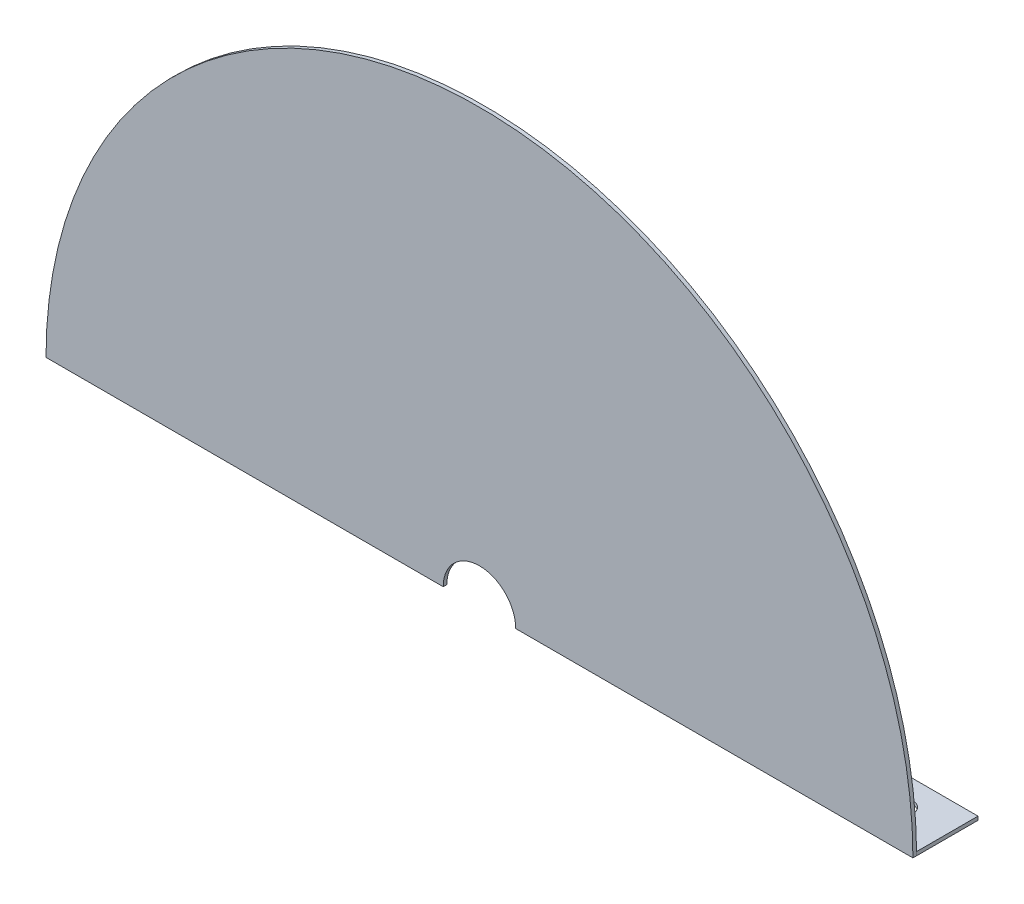
SolidWorks part; units mm, degrees
material "Plain Carbon Steel"
ref_plane "Front Plane" through (0, 0, 0) normal (0, 0, 1) x (1, 0, 0)
ref_plane "Top Plane" through (0, 0, 0) normal (0, 1, 0) x (1, 0, 0)
ref_plane "Right Plane" through (0, 0, 0) normal (1, 0, 0) x (0, 0, -1)
sketch "Plate shape" plane through (0, 0, 0) normal (0, 0, 1) x (1, 0, 0)
  line L3 (-154.3999, 0) -> (210.7061, 0) construction
  line L4 (0, 179.3189) -> (-179.3189, 179.3189)
  line L5 (0, 179.3189) -> (179.3189, 179.3189)
  line L9 (0, 179.3189) -> (0, 0) construction
  line L10 (0, 179.3189) -> (30, 179.3189) construction
  line L11 (30, 179.3189) -> (30, 356.1105) construction
  arc A0 (-179.3189, 179.3189) -> (179.3189, 179.3189) centre (0, 179.3189) cw
  arc A1 (179.3189, 179.3189) -> (-179.3189, 179.3189) centre (0, 179.3189) cw construction
  dimension "D1" = 179.3189
  dimension "D2" = 30
extrude "Outer casing" add sketch "Plate shape" along normal blind 1.5189
sketch "Sketch1" plane through (0, 0, 1.5189) normal (0, 0, 1) x (1, 0, 0)
  circle A0 centre (0, 179.3189) radius 179.3189 construction
  arc A1 (179.3189, 179.3189) -> (-179.3189, 179.3189) centre (0, 179.3189) ccw construction
  circle A2 centre (0, 179.3189) radius 15
  dimension "D1" = 30
extrude "Inner Cutout" cut sketch "Sketch1" against normal blind 20
sketch "Sketch3" plane through (0, 0, 1.5189) normal (0, 0, 1) x (1, 0, 0)
  line L0 (30, 179.3189) -> (30, 356.1105) construction
  line L1 (15, 179.3189) -> (179.3189, 179.3189) construction
  line L2 (-15, 179.3189) -> (15, 179.3189) construction
  arc A0 (179.3189, 179.3189) -> (-179.3189, 179.3189) centre (0, 179.3189) ccw construction
  point P11 (0, 179.3189)
  dimension "D1" = 30
sketch "Sketch4" plane through (0, 0, 0) normal (0, 0, -1) x (-1, 0, 0)
  line L0 (-179.3189, 179.3189) -> (-103.1189, 179.3189)
  line L1 (-15, 179.3189) -> (-179.3189, 179.3189) construction
  line L2 (-103.1189, 179.3189) -> (-103.1189, 180.8378)
  line L3 (-103.1189, 180.8378) -> (-179.3189, 180.8378)
  line L4 (-179.3189, 180.8378) -> (-179.3189, 179.3189)
  line L5 (179.3189, 179.3189) -> (103.1189, 179.3189)
  line L7 (179.3189, 179.3189) -> (15, 179.3189) construction
  line L8 (103.1189, 179.3189) -> (103.1189, 180.8378)
  line L9 (103.1189, 180.8378) -> (179.3189, 180.8378)
  line L10 (179.3189, 180.8378) -> (179.3189, 179.3189)
  dimension "D1" = 1.5189
  dimension "D2" = 76.2
  dimension "D3" = 1.5189
  dimension "D4" = 76.2
extrude "Boss-Extrude1" add sketch "Sketch4" along normal blind 25.4
sketch "Sketch5" plane through (0, 180.8378, 0) normal (0, 1, 0) x (1, 0, 0)
  line L0 (179.3189, 12.7) -> (103.1189, 12.7) construction
  line L1 (179.3189, 25.4) -> (179.3189, 0) construction
  line L2 (103.1189, 25.4) -> (103.1189, 0) construction
  line L3 (0, -55) -> (0, 55) construction
  circle A0 centre (160.2689, 12.7) radius 4.7625
  circle A1 centre (122.1689, 12.7) radius 4.7625
  circle A2 centre (-160.2689, 12.7) radius 4.7625
  circle A3 centre (-122.1689, 12.7) radius 4.7625
  dimension "D3" = 9.525
  dimension "D1" = 38.1
  dimension "D2" = 19.05
extrude "Cut-Extrude1" cut sketch "Sketch5" against normal through all
